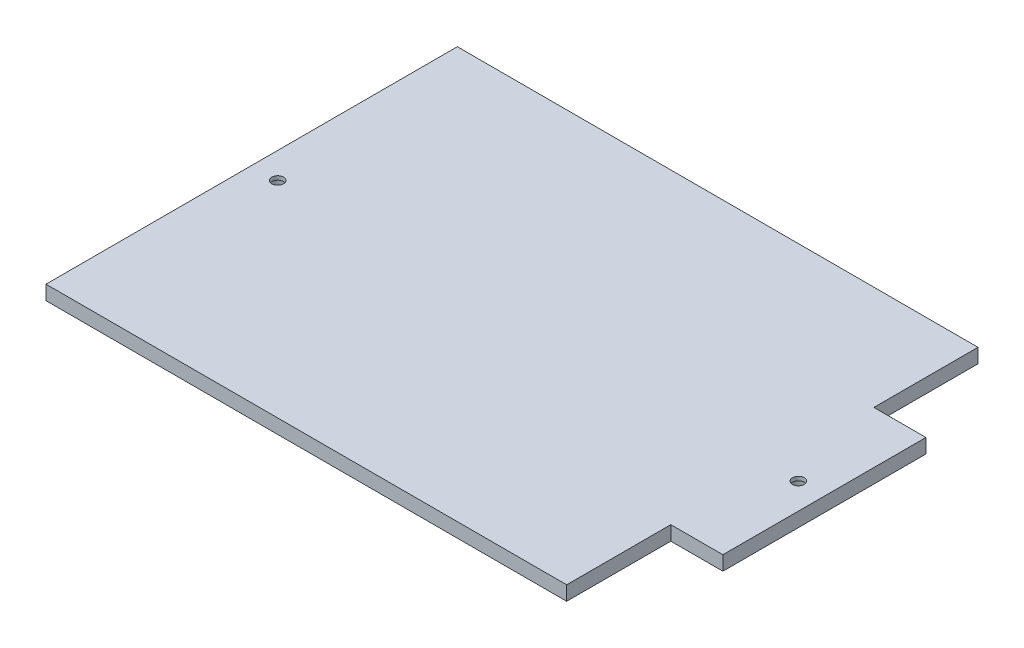
SolidWorks part; units mm, degrees
ref_plane "Front Plane" through (0, 0, 0) normal (0, 0, 1) x (1, 0, 0)
ref_plane "Top Plane" through (0, 0, 0) normal (0, 1, 0) x (1, 0, 0)
ref_plane "Right Plane" through (0, 0, 0) normal (1, 0, 0) x (0, 0, -1)
sketch "Sketch1" plane through (0, 0, 0) normal (0, 1, 0) x (1, 0, 0)
  line L1 (-110, 79) -> (110, 79)
  line L2 (-110, 79) -> (-110, -79)
  line L3 (-110, -79) -> (110, -79)
  line L4 (110, 79) -> (110, -79)
  line L5 (-110, 79) -> (110, -79) construction
  line L6 (-110, -79) -> (110, 79) construction
  point P0 (0, 0)
  dimension "D1" = 220
  dimension "D2" = 158
extrude "Boss-Extrude1" add sketch "Sketch1" along normal blind 5.5
sketch "Sketch2" plane through (0, 0, 0) normal (0, 1, 0) x (1, 0, 0)
  point P0 (100, 0)
  dimension "D1" = 100
sketch "Sketch4" [suppressed] plane through (0, 4, 0) normal (0, 1, 0) x (1, 0, 0)
  line L0 (115, -79) -> (115, -59)
  line L1 (115, -79) -> (115, 79) construction
  line L2 (115, -79) -> (95, -79)
  line L3 (-115, -79) -> (115, -79) construction
  line L4 (115, -59) -> (85.4514, -59) construction
  arc A0 (95, -79) -> (115, -59) centre (115, -79) cw
  dimension "D1" = 20
hole_wizard "CBORE for M4 SHCS1" positions "Sketch2" profile "Sketch5" counterbore size "M4" standard "ANSI Metric" end condition through all
sketch "Sketch5" plane through (100, 0, 0) normal (1, 0, 0) x (0, 0, -1)
  line L0 (0, 0) -> (0, 5.5)
  line L1 (0, 5.5) -> (2.25, 5.5)
  line L3 (2.25, 5.5) -> (2.25, 4)
  line L4 (2.25, 4) -> (4, 4)
  line L5 (4, 4) -> (4, 0)
  line L7 (4, 0) -> (0, 0)
  line L11 (0, -6.35) -> (0, 107.95) construction
  dimension "Thru Hole Dia." = 4.5
  dimension "Thru Hole Depth" = 5.5
  dimension "C'Bore Dia." = 8
  dimension "C'Bore Depth" = 4
mirror "Mirror2" about plane through (0, 0, 0) normal (1, 0, 0) of "CBORE for M4 SHCS1"
sketch "Sketch6" plane through (0, 5.5, 0) normal (0, 1, 0) x (1, 0, 0)
  line L1 (110, 79) -> (90, 79)
  line L2 (110, 79) -> (110, 39)
  line L3 (110, 39) -> (90, 39)
  line L4 (90, 79) -> (90, 39)
  dimension "D1" = 20
  dimension "D2" = 40
extrude "Cut-Extrude2" cut sketch "Sketch6" against normal through all
mirror "Mirror3" about plane through (0, 0, 0) normal (0, 0, 1) of "Cut-Extrude2"
